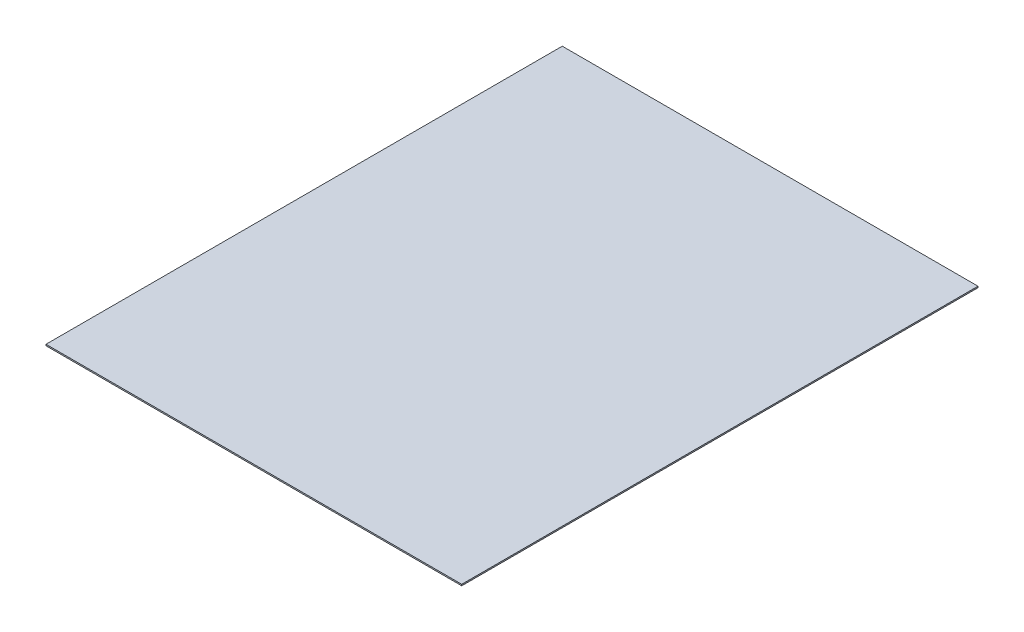
SolidWorks part; units mm, degrees
ref_plane "Front Plane" through (0, 0, 0) normal (0, 0, 1) x (1, 0, 0)
ref_plane "Top Plane" through (0, 0, 0) normal (0, 1, 0) x (1, 0, 0)
ref_plane "Right Plane" through (0, 0, 0) normal (1, 0, 0) x (0, 0, -1)
sketch "Sketch1" plane through (0, 0, 0) normal (0, 1, 0) x (1, 0, 0)
  line L0 (-348.1526, -209.8445) -> (-42.1526, -209.8445)
  line L5 (-42.1526, -209.8445) -> (-42.1526, 170.1555) construction
  line L6 (-348.1526, -209.8445) -> (-348.1526, 170.1555) construction
  line L7 (-42.1526, -209.8445) -> (-42.1526, 170.1555)
  line L8 (-348.1526, -209.8445) -> (-348.1526, 170.1555)
  line L9 (-348.1526, 170.1555) -> (-42.1526, 170.1555)
extrude "Boss-Extrude1" add sketch "Sketch1" along normal blind 1
